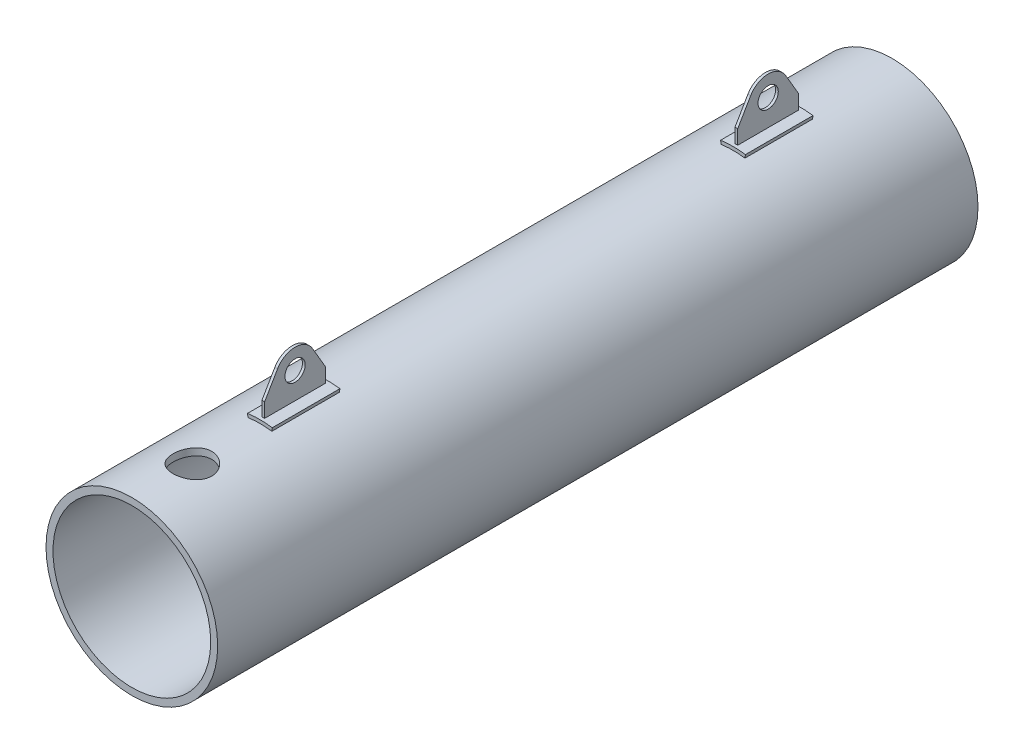
SolidWorks part; units mm, degrees
material "AISI 304"
ref_plane "Front Plane" through (0, 0, 0) normal (0, 0, 1) x (1, 0, 0)
ref_plane "Top Plane" through (0, 0, 0) normal (0, 1, 0) x (1, 0, 0)
ref_plane "Right Plane" through (0, 0, 0) normal (1, 0, 0) x (0, 0, -1)
sketch "Sketch1" plane through (0, 0, 0) normal (0, 0, 1) x (1, 0, 0)
  circle A0 centre (0, 0) radius 233.38
  circle A1 centre (0, 0) radius 254
  dimension "D1" = 508
  dimension "D2" = 466.76
extrude "Boss-Extrude1" add sketch "Sketch1" against normal blind 2250
sketch "Sketch2" plane through (0, 0, 0) normal (0, 1, 0) x (1, 0, 0)
  circle A0 centre (0, 179) radius 57.25
  dimension "D1" = 114.5
  dimension "D2" = 179
extrude "Cut-Extrude1" cut sketch "Sketch2" along normal up to surface (254 mm away)
sketch "Sketch3" plane through (0, 0, 0) normal (0, 1, 0) x (1, 0, 0)
  circle A0 centre (0, 2049) radius 57.25
  dimension "D2" = 114.5
  dimension "D1" = 2049
extrude "Cut-Extrude2" cut sketch "Sketch3" against normal up to surface (254 mm away)
sketch "Sketch4" plane through (0, 0, 0) normal (0, 1, 0) x (1, 0, 0)
  circle A0 centre (0, 649) radius 24.5
  dimension "D2" = 49
  dimension "D1" = 649
extrude "Cut-Extrude3" cut sketch "Sketch4" against normal up to surface (254 mm away)
sketch "Sketch5" plane through (0, 0, 0) normal (1, 0, 0) x (0, 0, -1)
  line L0 (2250, 254) -> (236.25, 254) construction
  line L1 (379, 254) -> (579, 254)
  line L2 (379, 254) -> (379, 264)
  line L3 (379, 264) -> (579, 264)
  line L4 (579, 254) -> (579, 264)
  line L5 (0, 0) -> (2250, 0) construction
  line L6 (1779, 254) -> (1979, 254)
  line L7 (1779, 254) -> (1779, 264)
  line L8 (1779, 264) -> (1979, 264)
  line L9 (1979, 254) -> (1979, 264)
  line L10 (2250, -254) -> (2250, 254) construction
  point P6 (479, 264)
  point P12 (1879, 264)
  dimension "D1" = 200
  dimension "D2" = 10
  dimension "D3" = 479
  dimension "D4" = 200
  dimension "D5" = 10
  dimension "D6" = 1400
revolve "Revolve1" add sketch "Sketch5" angle 16 mid plane about L5
sketch "Sketch6" plane through (0, 0, 0) normal (1, 0, 0) x (0, 0, -1)
  line L0 (379, 251.5281) -> (579, 251.5281) construction
  line L1 (479, 341.5281) -> (479, 251.5281) construction
  line L2 (479, 251.5281) -> (569, 251.5281)
  line L3 (479, 251.5281) -> (389, 251.5281)
  line L4 (389, 251.5281) -> (389, 306.5281)
  line L5 (569, 251.5281) -> (569, 306.5281)
  line L6 (389, 306.5281) -> (427.2151, 371.832)
  line L7 (569, 306.5281) -> (530.7849, 371.832)
  line L8 (1969, 251.5281) -> (1969, 306.5281)
  line L9 (1969, 306.5281) -> (1930.7849, 371.832)
  line L10 (1789, 306.5281) -> (1827.2151, 371.832)
  line L11 (1789, 251.5281) -> (1789, 306.5281)
  line L12 (1879, 251.5281) -> (1789, 251.5281)
  line L13 (1879, 251.5281) -> (1969, 251.5281)
  circle A0 centre (479, 341.5281) radius 30
  arc A1 (530.7849, 371.832) -> (427.2151, 371.832) centre (479, 341.5281) ccw
  circle A2 centre (1879, 341.5281) radius 30
  arc A3 (1930.7849, 371.832) -> (1827.2151, 371.832) centre (1879, 341.5281) ccw
  point P5 (479, 251.5281)
  dimension "D1" = 60
  dimension "D2" = 120
  dimension "D3" = 90
  dimension "D4" = 90
  dimension "D5" = 90
  dimension "D6" = 55
  dimension "D7" = 2
extrude "Boss-Extrude2" add sketch "Sketch6" along normal mid plane 8
